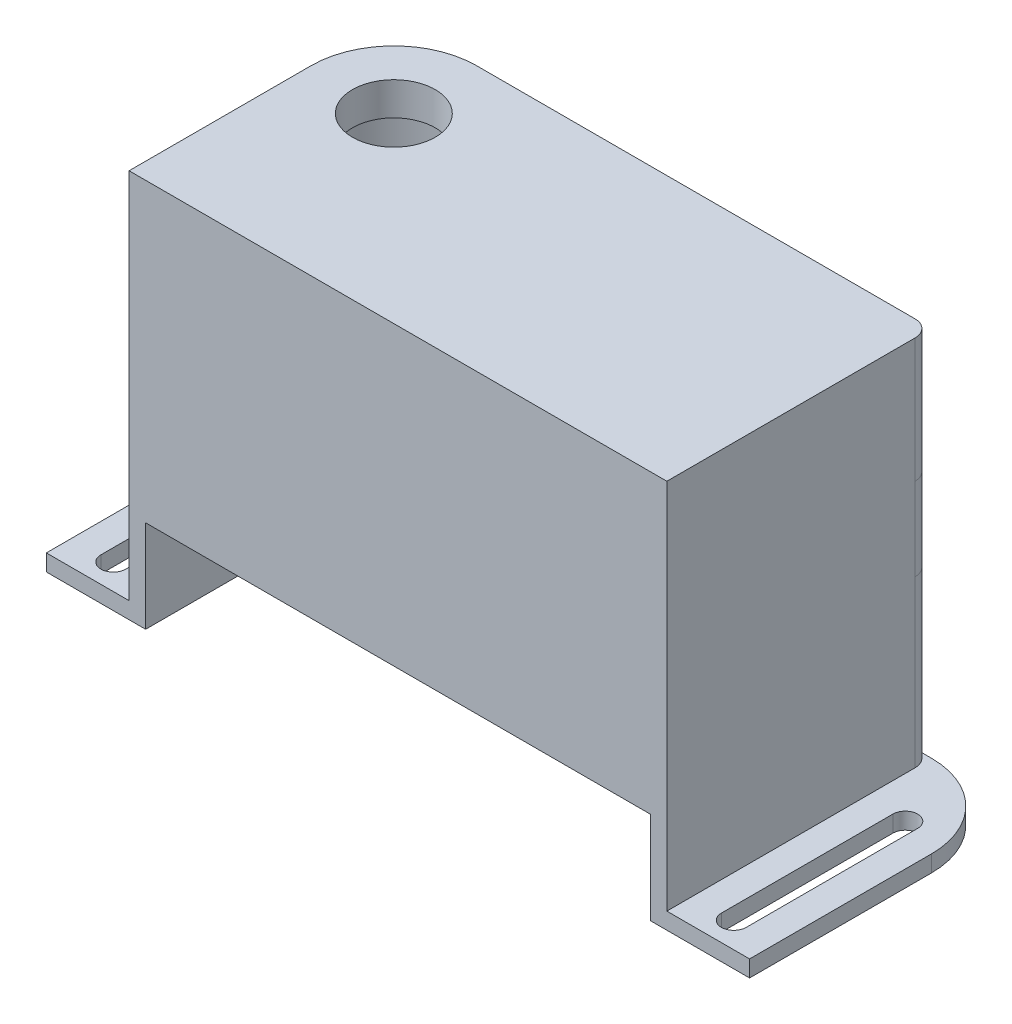
SolidWorks part; units mm, degrees
ref_plane "Front Plane" through (0, 0, 0) normal (0, 0, 1) x (1, 0, 0)
ref_plane "Top Plane" through (0, 0, 0) normal (0, 1, 0) x (1, 0, 0)
ref_plane "Right Plane" through (0, 0, 0) normal (1, 0, 0) x (0, 0, -1)
sketch "Sketch1" plane through (0, 0, 0) normal (0, 1, 0) x (1, 0, 0)
  point P0 (0, 0)
sketch "Sketch2" plane through (0, 0, 0) normal (0, 1, 0) x (1, 0, 0)
  line L1 (-42.5, -16) -> (42.5, -16)
  line L2 (-42.5, -16) -> (-42.5, 16)
  line L3 (-42.5, 16) -> (42.5, 16)
  line L4 (42.5, -16) -> (42.5, 16)
  line L5 (-42.5, -16) -> (42.5, 16) construction
  line L6 (-42.5, 16) -> (42.5, -16) construction
  point P0 (0, 0)
  dimension "D1" = 32
  dimension "D2" = 85
extrude "Boss-Extrude1" add sketch "Sketch2" along normal blind 2
sketch "Sketch3" plane through (0, 2, 0) normal (0, 1, 0) x (1, 0, 0)
  line L0 (-42.5, -16) -> (42.5, -16) construction
  line L1 (-32.5, 16) -> (32.5, 16)
  line L2 (-32.5, 16) -> (-32.5, -16)
  line L3 (-32.5, -16) -> (32.5, -16)
  line L4 (32.5, 16) -> (32.5, -16)
  line L5 (-32.5, 16) -> (32.5, -16) construction
  line L6 (-32.5, -16) -> (32.5, 16) construction
  point P0 (0, 0)
  dimension "D1" = 65
extrude "Boss-Extrude2" add sketch "Sketch3" along normal blind 45 contours L2 L3 L4 L1
sketch "Sketch4" plane through (0, 0, 0) normal (0, -1, 0) x (1, 0, 0)
  line L1 (-30.5, -14) -> (30.5, -14)
  line L2 (-30.5, -14) -> (-30.5, 14)
  line L3 (-30.5, 14) -> (30.5, 14)
  line L4 (30.5, -14) -> (30.5, 14)
  line L5 (-30.5, -14) -> (30.5, 14) construction
  line L6 (-30.5, 14) -> (30.5, -14) construction
  point P0 (0, 0)
  dimension "D1" = 61
  dimension "D2" = 28
extrude "Cut-Extrude1" cut sketch "Sketch4" against normal blind 43
fillet "Fillet1" radius 10 1 edges at (-32.5, 24.5, -16)
fillet "Fillet2" radius 2 1 edges at (32.5, 24.5, -16)
fillet "Fillet3" radius 10 1 edges at (-42.5, 1, -16)
fillet "Fillet4" radius 10 1 edges at (42.5, 1, -16)
fillet "Fillet5" radius 10 1 edges at (-30.5, 21.5, -14)
fillet "Fillet6" radius 2 1 edges at (30.5, 21.5, -14)
sketch "Sketch5" plane through (0, 0, 16) normal (0, 0, 1) x (1, 0, 0)
  line L1 (-30.5, -11.1506) -> (30.5, -11.1506)
  line L2 (-30.5, -11.1506) -> (-30.5, 11.1506)
  line L3 (-30.5, 11.1506) -> (30.5, 11.1506)
  line L4 (30.5, -11.1506) -> (30.5, 11.1506)
  line L5 (-30.5, -11.1506) -> (30.5, 11.1506) construction
  line L6 (-30.5, 11.1506) -> (30.5, -11.1506) construction
  point P0 (0, 0)
  dimension "D1" = 61
extrude "Cut-Extrude2" cut sketch "Sketch5" against normal blind 10
sketch "Sketch6" plane through (0, 2, 0) normal (0, 1, 0) x (1, 0, 0)
  line L0 (37.5, 7.8166) -> (37.5, -12.9044) construction
  line L1 (39, 7.8166) -> (39, -12.9044)
  line L2 (36, 7.8166) -> (36, -12.9044)
  line L3 (-37.5, 7.8166) -> (-37.5, -12.9044) construction
  line L4 (-36, 7.8166) -> (-36, -12.9044)
  line L5 (-39, 7.8166) -> (-39, -12.9044)
  line L6 (-32.5, 6) -> (-32.5, -16) construction
  line L7 (32.5, 14) -> (32.5, -16) construction
  arc A0 (39, 7.8166) -> (36, 7.8166) centre (37.5, 7.8166) ccw
  arc A1 (36, -12.9044) -> (39, -12.9044) centre (37.5, -12.9044) ccw
  arc A2 (-36, 7.8166) -> (-39, 7.8166) centre (-37.5, 7.8166) ccw
  arc A3 (-39, -12.9044) -> (-36, -12.9044) centre (-37.5, -12.9044) ccw
  point P2 (37.5, -2.5439)
  point P7 (-37.5, -2.5439)
  dimension "D1" = 3
  dimension "D2" = 3
  dimension "D3" = 3.5
  dimension "D4" = 3.5
extrude "Cut-Extrude3" cut sketch "Sketch6" against normal blind 10
sketch "Sketch7" plane through (0, 47, 0) normal (0, 1, 0) x (1, 0, 0)
  line L0 (-22.5, 16) -> (30.5, 16) construction
  line L1 (-32.5, 6) -> (-32.5, -16) construction
  circle A0 centre (-22.5, 6) radius 5
  dimension "D1" = 10
  dimension "D2" = 10
extrude "Cut-Extrude4" cut sketch "Sketch7" against normal blind 10
ref_plane "Plane1" through (0, 22, 0) normal (0, 1, 0) x (1, 0, 0)
sketch "Sketch8" plane through (0, 22, 0) normal (0, 1, 0) x (1, 0, 0)
  line L0 (-22.5, 16) -> (30.5, 16) construction
  line L1 (-1.5, 16) -> (32.5, 16)
  line L2 (-1.5, 16) -> (-1.5, 4)
  line L3 (-1.5, 4) -> (32.5, 4)
  line L4 (32.5, 16) -> (32.5, 4)
  line L5 (32.5, 14) -> (32.5, -16) construction
  line L7 (3.5, 16) -> (25.5, 16)
  line L8 (3.5, 16) -> (3.5, 4)
  line L9 (3.5, 4) -> (25.5, 4)
  line L10 (25.5, 16) -> (25.5, 4)
  point P12 (32.5, 10)
  dimension "D1" = 12
  dimension "D2" = 34
  dimension "D3" = 5
  dimension "D4" = 7
extrude "Boss-Extrude3" add sketch "Sketch8" along normal blind 10 contours L1 L10 L3 L4 | L8 L1 L2 L3
fillet "Fillet8" radius 2 1 edges at (32.5, 27, -16)
sketch "Sketch9" plane through (0, 22, 0) normal (0, -1, 0) x (1, 0, 0)
  line L0 (-20.5, -14) -> (28.5, -14) construction
  line L1 (3.5, -14) -> (3.5, -4) construction
  line L2 (25.5, -14) -> (25.5, -4) construction
  circle A0 centre (1, -8) radius 1
  circle A1 centre (28, -8) radius 1
  dimension "D1" = 6
  dimension "D3" = 2.5
  dimension "D2" = 2.5
extrude "Cut-Extrude5" cut sketch "Sketch9" against normal blind 10
sketch "Sketch10" plane through (0, 0, -14) normal (0, 0, 1) x (1, 0, 0)
  line L0 (-1.5, 22) -> (3.5, 22) construction
  line L1 (-8.0879, 32) -> (-5.0879, 32)
  line L2 (-8.0879, 32) -> (-8.0879, 22)
  line L3 (-8.0879, 22) -> (-5.0879, 22)
  line L4 (-5.0879, 32) -> (-5.0879, 22)
  dimension "D1" = 3
  dimension "D2" = 10
  dimension "D3" = 0
extrude "Boss-Extrude4" add sketch "Sketch10" along normal blind 10
sketch "Sketch11" plane through (-8.0879, 0, 0) normal (-1, 0, 0) x (0, 0, 1)
  line L0 (-14, 32) -> (-14, 22) construction
  line L1 (-14, 30) -> (-6, 30)
  line L2 (-14, 30) -> (-14, 24)
  line L3 (-14, 24) -> (-6, 24)
  line L4 (-6, 30) -> (-6, 24)
  line L5 (-4, 22) -> (-14, 22) construction
  line L6 (-4, 32) -> (-14, 32) construction
  line L7 (-4, 32) -> (-4, 22) construction
  dimension "D1" = 2
  dimension "D2" = 2
  dimension "D3" = 2
extrude "Cut-Extrude6" cut sketch "Sketch11" against normal blind 5
